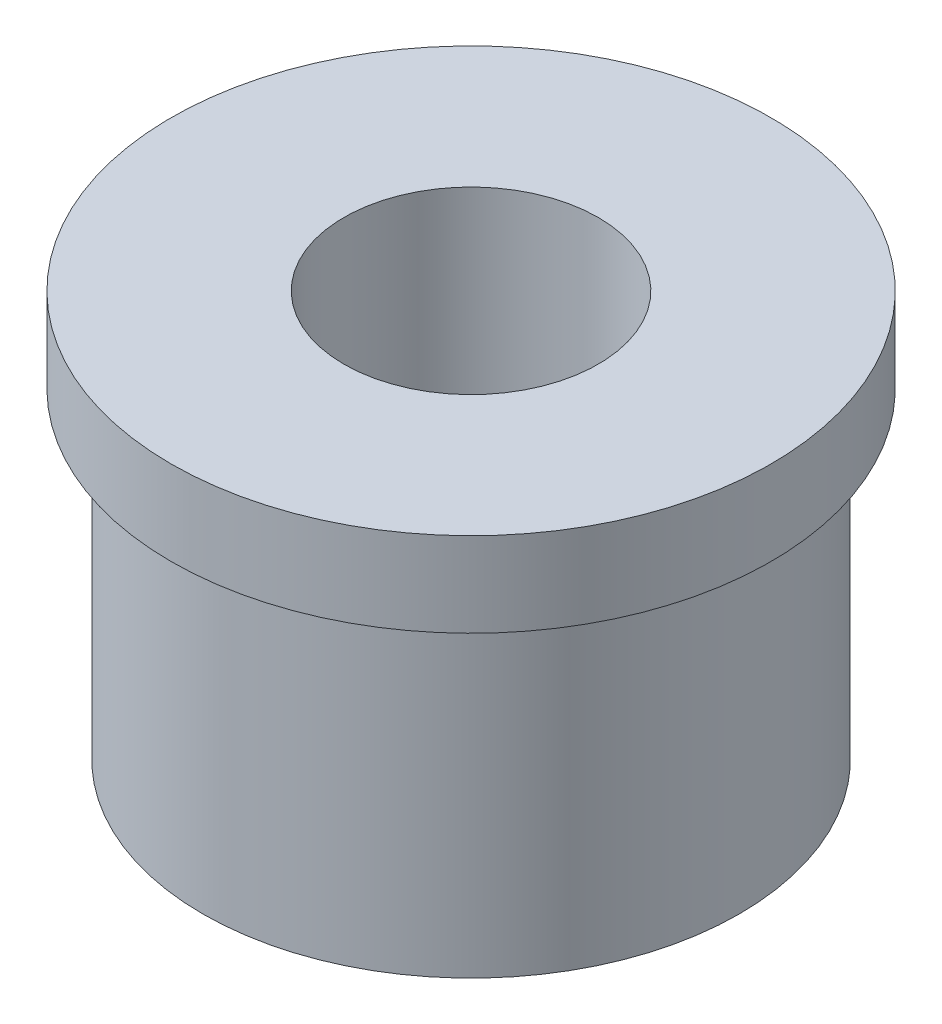
SolidWorks part; units mm, degrees
material "Aluminum Bronze"
ref_plane "Front Plane" through (0, 0, 0) normal (0, 0, 1) x (1, 0, 0)
ref_plane "Top Plane" through (0, 0, 0) normal (0, 1, 0) x (1, 0, 0)
ref_plane "Right Plane" through (0, 0, 0) normal (1, 0, 0) x (0, 0, -1)
sketch "Sketch1" plane through (0, 0, 0) normal (0, 1, 0) x (1, 0, 0)
  circle A0 centre (0, 0) radius 3.01
  circle A1 centre (0, 0) radius 6.35
  dimension "D1" = 6.02
  dimension "D2" = 12.7
extrude "Boss-Extrude1" add sketch "Sketch1" along normal blind 9.6
sketch "Sketch2" plane through (0, 9.6, 0) normal (0, 1, 0) x (-1, 0, 0)
  circle A0 centre (0, 0) radius 7.1
  circle A1 centre (0, 0) radius 5
  dimension "D1" = 10
  dimension "D2" = 14.2
extrude "Boss-Extrude2" add sketch "Sketch2" against normal blind 2
